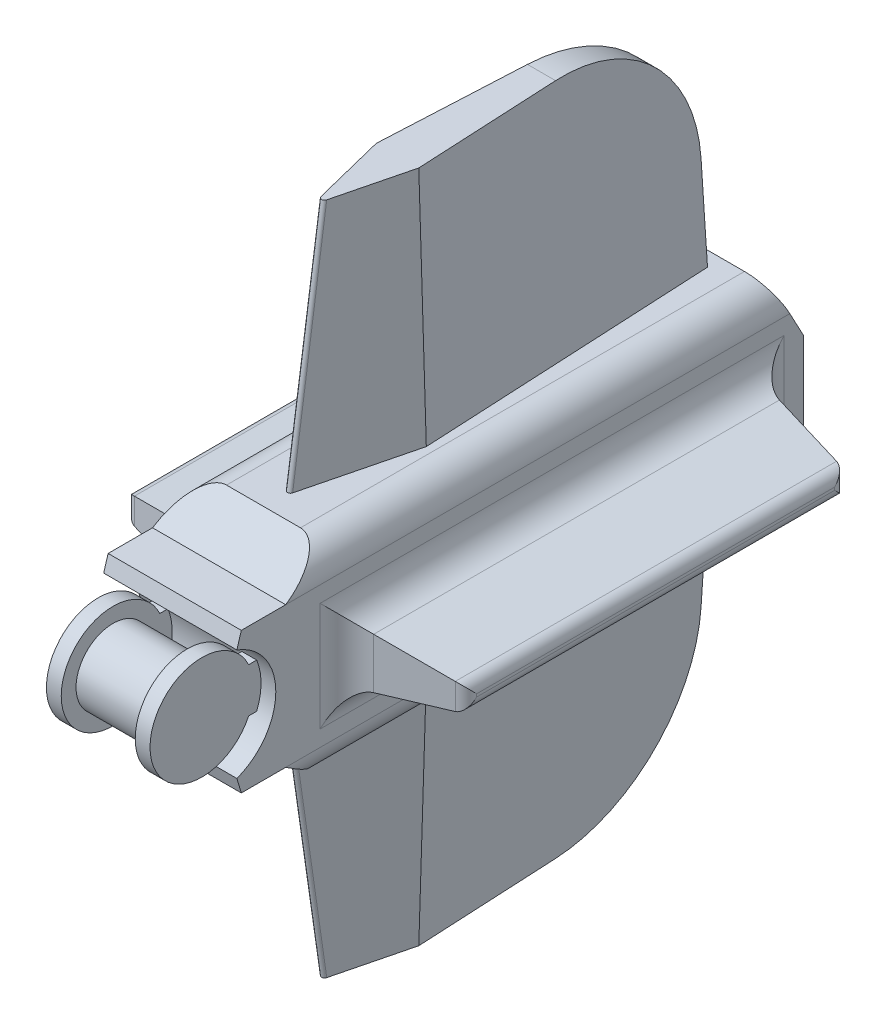
SolidWorks part; units mm, degrees
ref_plane "Front Plane" through (0, 0, 0) normal (0, 0, 1) x (1, 0, 0)
ref_plane "Top Plane" through (0, 0, 0) normal (0, 1, 0) x (1, 0, 0)
ref_plane "Right Plane" through (0, 0, 0) normal (1, 0, 0) x (0, 0, -1)
sketch "Sketch1" plane through (0, 0, 0) normal (1, 0, 0) x (0, 0, -1)
  circle A0 centre (0, 0) radius 3.175
  dimension "D1" = 6.35
extrude "Boss-Extrude1" add sketch "Sketch1" along normal mid plane 6.35
sketch "Sketch2" plane through (3.175, 0, 0) normal (1, 0, 0) x (0, 0, -1)
  circle A0 centre (0, 0) radius 4.445
  dimension "D1" = 8.89
extrude "Boss-Extrude2" add sketch "Sketch2" along normal blind 1.27
mirror "Mirror1" about plane through (0, 0, 0) normal (1, 0, 0) of "Boss-Extrude2"
sketch "Sketch3" plane through (4.445, 0, 0) normal (1, 0, 0) x (0, 0, -1)
  line L1 (0, 1.905) -> (6.35, 1.905)
  line L2 (0, 1.905) -> (0, -1.905)
  line L3 (0, -1.905) -> (6.35, -1.905)
  line L4 (6.35, 1.905) -> (6.35, -1.905)
  point P4 (0, 0)
  dimension "D1" = 3.81
  dimension "D2" = 6.35
extrude "Boss-Extrude3" add sketch "Sketch3" against normal blind 1.27
mirror "Mirror2" about plane through (0, 0, 0) normal (1, 0, 0) of "Boss-Extrude3"
sketch "Sketch4" plane through (-3.175, 0, 0) normal (1, 0, 0) x (0, 0, -1)
  line L0 (1.7375, 4.7736) -> (0, 0) construction
  line L1 (0, 0) -> (5.08, 0) construction
  line L2 (1.7375, 4.7736) -> (2.1185, 6.0436)
  line L3 (2.1185, 6.0436) -> (5.9285, 6.0436)
  line L4 (0, 0) -> (1.7375, -4.7736) construction
  line L5 (5.9285, 6.0436) -> (9.7385, 8.5836)
  line L6 (9.7385, 8.5836) -> (47.8385, 8.5836)
  line L7 (47.8385, 8.5836) -> (50.3785, 3.81)
  line L8 (50.3785, 3.81) -> (50.3785, -3.81)
  line L9 (50.3785, 0) -> (5.08, 0) construction
  line L10 (47.8385, -8.5836) -> (50.3785, -3.81)
  line L11 (9.7385, -8.5836) -> (47.8385, -8.5836)
  line L12 (5.9285, -6.0436) -> (9.7385, -8.5836)
  line L13 (2.1185, -6.0436) -> (5.9285, -6.0436)
  line L14 (1.7375, -4.7736) -> (2.1185, -6.0436)
  arc A0 (1.7375, 4.7736) -> (1.7375, -4.7736) centre (0, 0) cw
  dimension "D1" = 5.08
  dimension "D2" = 140
  dimension "D3" = 1.27
  dimension "D4" = 0.381
  dimension "D5" = 3.81
  dimension "D6" = 3.81
  dimension "D7" = 2.54
  dimension "D8" = 38.1
  dimension "D9" = 7.62
  dimension "D10" = 2.54
extrude "Boss-Extrude4" add sketch "Sketch4" against normal blind 2.54 and the other way blind 8.89
sketch "Sketch5" plane through (0, 0, -50.3785) normal (0, 0, -1) x (-1, 0, 0)
  circle A0 centre (0, 0) radius 3.175
  dimension "D1" = 6.35
extrude "Cut-Extrude1" cut sketch "Sketch5" against normal blind 12.7
fillet "Fillet1" radius 2.54 4 edges at (5.715, -8.5836, -28.7885) (-5.715, -8.5836, -28.7885) (-5.715, 8.5836, -28.7885) (5.715, 8.5836, -28.7885)
sketch "Sketch6" plane through (5.715, 0, 0) normal (1, 0, 0) x (0, 0, -1)
  line L0 (50.3785, -3.81) -> (50.3785, 3.81) construction
  line L1 (11.0085, 2.54) -> (46.5685, 2.54)
  line L2 (11.0085, 2.54) -> (11.0085, -2.54)
  line L3 (11.0085, -2.54) -> (46.5685, -2.54)
  line L4 (46.5685, 2.54) -> (46.5685, -2.54)
  point P4 (11.0085, 0)
  point P6 (50.3785, 0)
  dimension "D1" = 3.81
  dimension "D2" = 5.08
  dimension "D3" = 35.56
extrude "Boss-Extrude5" add sketch "Sketch6" along normal blind 8.89 draft 10
mirror "Mirror3" about plane through (0, 0, 0) normal (1, 0, 0) of "Boss-Extrude5"
fillet "Fillet2" radius 1.016 8 edges at (-14.605, -0.9725, -28.7885) (-14.605, 0, -45.0009) (-14.605, 0.9725, -28.7885) (-14.605, 0, -12.576) (14.605, 0.9725, -28.7885) (14.605, 0, -45.0009) (14.605, -0.9725, -28.7885) (14.605, 0, -12.576)
fillet "Fillet3" radius 2.54 8 edges at (5.715, -2.54, -28.7885) (5.715, 0, -11.0085) (5.715, 0, -46.5685) (5.715, 2.54, -28.7885) (-5.715, 0, -11.0085) (-5.715, 0, -46.5685) (-5.715, -2.54, -28.7885) (-5.715, 2.54, -28.7885)
sketch "Sketch7" plane through (0, 8.5836, 0) normal (0, 1, 0) x (1, 0, 0)
  line L0 (0, 9.7385) -> (0, 47.8385) construction
  line L1 (3.175, 9.7385) -> (-3.175, 9.7385) construction
  line L2 (3.175, 47.8385) -> (-3.175, 47.8385) construction
  line L3 (-1.27, 46.5685) -> (1.27, 46.5685)
  line L4 (1.27, 46.5685) -> (2.54, 21.1685)
  line L5 (2.54, 21.1685) -> (0, 11.0085)
  line L6 (0, 11.0085) -> (-2.54, 21.1685)
  line L7 (-2.54, 21.1685) -> (-1.27, 46.5685)
  point P8 (0, 46.5685)
  dimension "D1" = 2.54
  dimension "D2" = 1.27
  dimension "D3" = 1.27
  dimension "D4" = 2.54
  dimension "D5" = 25.4
extrude "Boss-Extrude6" add sketch "Sketch7" along normal blind 20.32 draft 2
mirror "Mirror4" about plane through (0, 0, 0) normal (0, 1, 0) of "Boss-Extrude6"
fillet "Fillet4" radius 0.254 2 edges at (0, -18.7436, -12.4713) (0, 18.7436, -12.4713)
fillet "Fillet5" radius 12.7 2 edges at (0, -28.9036, -45.8589) (0, 28.9036, -45.8589)
